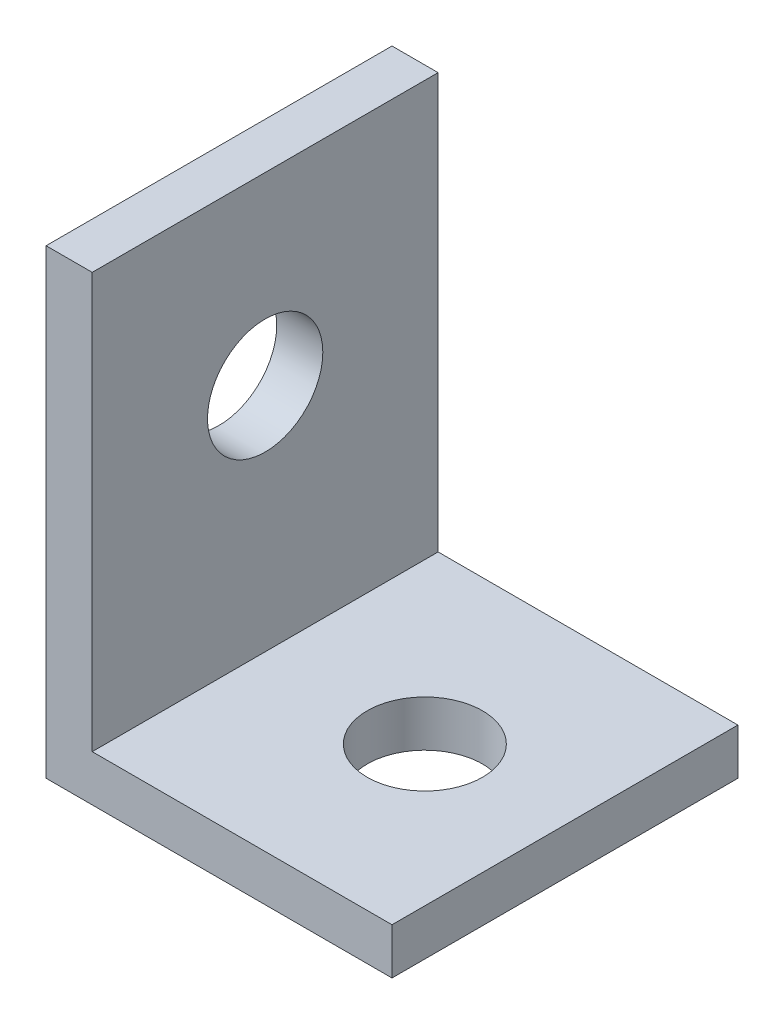
SolidWorks part; units mm, degrees
ref_plane "Front" through (0, 0, 0) normal (0, 0, 1) x (1, 0, 0)
ref_plane "Top" through (0, 0, 0) normal (0, 1, 0) x (1, 0, 0)
ref_plane "Right" through (0, 0, 0) normal (1, 0, 0) x (0, 0, -1)
sketch "Sketch2" plane through (0, 0, 0) normal (0, 0, 1) x (1, 0, 0)
  line L2 (0, 0) -> (0, 25.4)
  line L3 (0, 25.4) -> (2.54, 25.4)
  line L4 (2.54, 2.54) -> (2.54, 25.4)
  line L5 (0, 0) -> (19.05, 0)
  line L7 (2.54, 2.54) -> (19.05, 2.54)
  line L8 (19.05, 0) -> (19.05, 2.54)
  point P3 (0, 0)
  point P9 (0, 0)
  point P10 (0, 0)
  point P11 (0, 0)
  point P12 (0, 0)
  dimension "D1" = 25.4
  dimension "D2" = 19.05
  dimension "D3" = 2.54
  dimension "D4" = 2.54
extrude "Boss-Extrude2" add sketch "Sketch2" along normal blind 19.05
sketch "Sketch3" plane through (2.54, 0, 0) normal (1, 0, 0) x (0, 0, -1)
  line L0 (-19.05, 25.4) -> (0, 25.4) construction
  line L1 (-19.05, 2.54) -> (0, 2.54) construction
  circle A0 centre (-9.525, 15.24) radius 3.175
  point P4 (-9.525, 25.4)
  dimension "D1" = 6.35
  dimension "D2" = 12.7
extrude "Cut-Extrude1" cut sketch "Sketch3" against normal blind 19.05
sketch "Sketch4" plane through (0, 2.54, 0) normal (0, 1, 0) x (1, 0, 0)
  line L2 (19.05, 0) -> (2.54, 0) construction
  line L3 (2.54, -19.05) -> (2.54, 0) construction
  circle A0 centre (11.3342, -9.525) radius 3.175
  point P4 (0, 0)
  point P5 (0, 0)
  dimension "D3" = 6.35
  dimension "D1" = 9.525
  dimension "D2" = 8.7942
extrude "Cut-Extrude2" cut sketch "Sketch4" against normal blind 19.05
